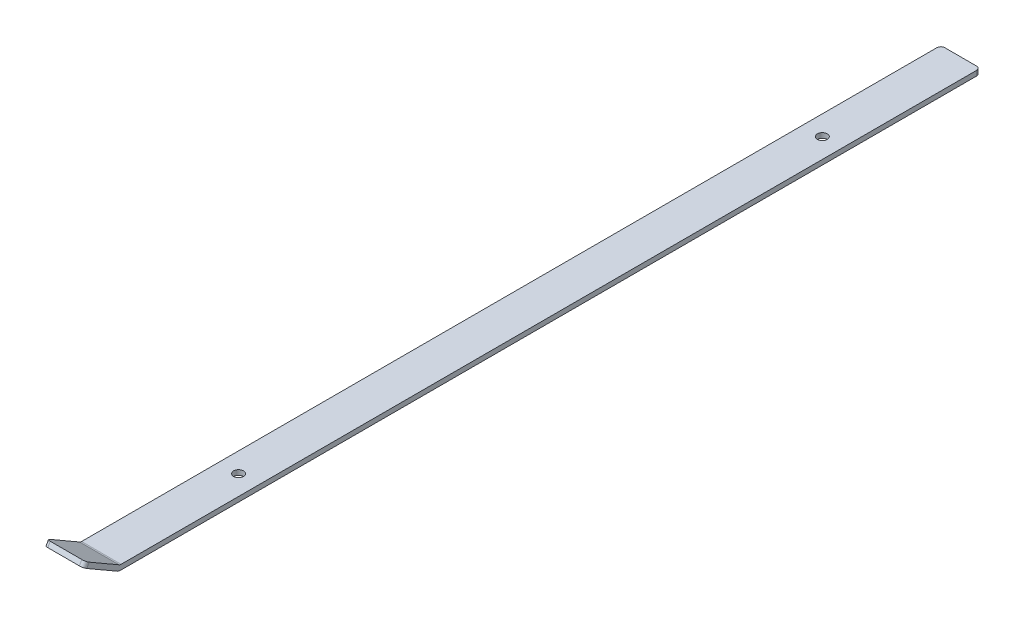
SolidWorks part; units mm, degrees
material "1023 Carbon Steel Sheet (SS)"
ref_plane "Front" through (0, 0, 0) normal (0, 0, 1) x (1, 0, 0)
ref_plane "Top" through (0, 0, 0) normal (0, 1, 0) x (1, 0, 0)
ref_plane "Right" through (0, 0, 0) normal (1, 0, 0) x (0, 0, -1)
sketch "Sketch1" plane through (0, 0, 0) normal (1, 0, 0) x (0, 0, -1)
  line L0 (0, 0) -> (-21.997, 12.7)
  line L1 (0, 0) -> (553.1612, 0)
  line L2 (0, 0) -> (0, -3.175) construction
  line L3 (0, -3.175) -> (553.1612, -3.175)
  line L4 (553.1612, 0) -> (553.1612, -3.175)
  line L5 (-21.997, 12.7) -> (-23.5845, 9.9504)
  line L6 (-23.5845, 9.9504) -> (-1.5875, -2.7496)
  arc A0 (0, -3.175) -> (-1.5875, -2.7496) centre (0, 0) cw
  dimension "D1" = 150
  dimension "D2" = 25.4
  dimension "D3" = 553.1612
  dimension "D4" = 3.175
extrude "Boss-Extrude1" add sketch "Sketch1" along normal blind 25.4
sketch "Sketch2" plane through (0, 0, 0) normal (0, 1, 0) x (1, 0, 0)
  line L0 (12.7, 0) -> (12.7, 19.1815) construction
  line L2 (25.4, 0) -> (0, 0) construction
  line L3 (25.4, 553.1612) -> (0, 553.1612) construction
  circle A0 centre (12.7, 88.9) radius 3.175
  circle A1 centre (12.7, 464.2612) radius 3.175
  point P3 (12.7, 0)
  dimension "D1" = 6.35
  dimension "D2" = 88.9
  dimension "D3" = 88.9
extrude "Cut-Extrude1" cut sketch "Sketch2" against normal through all
fillet "Fillet1" radius 2.54 5 edges at (0, -1.5875, -553.1612) (25.4, -1.5875, -553.1612) (0, 11.3252, 22.7908) (25.4, 11.3252, 22.7908) (12.7, 0, 0)
equation "\"12ion\"=3.48165"
